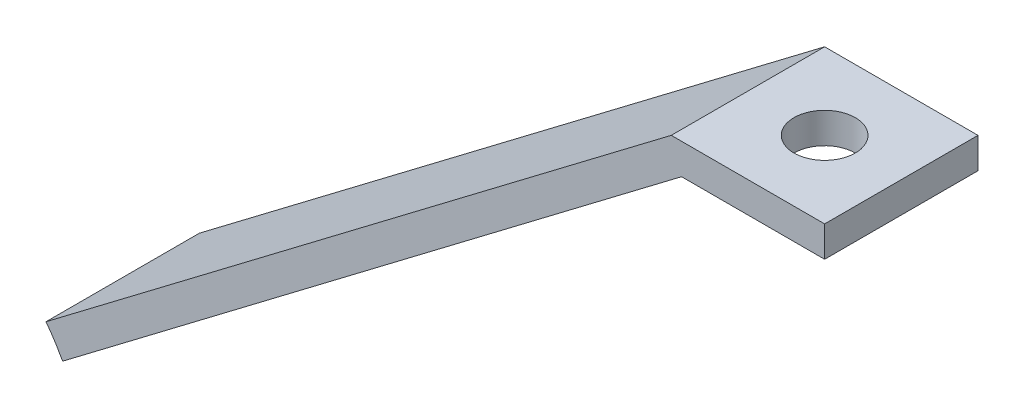
SolidWorks part; units mm, degrees
material "1.4113(X6CrMoS17-1)"
ref_plane "Płaszczyzna XY" through (0, 0, 0) normal (0, 0, 1) x (1, 0, 0)
ref_plane "Płaszczyzna XZ" through (0, 0, 0) normal (0, 1, 0) x (1, 0, 0)
ref_plane "Płaszczyzna YZ" through (0, 0, 0) normal (1, 0, 0) x (0, 0, -1)
ref_plane "Płaszczyzna1" through (0, 0, 502.9993) normal (0, 0, -1) x (-1, 0, 0)
sketch "Szkic1" plane through (0, 0, 502.9993) normal (0, 0, -1) x (-1, 0, 0)
  line L0 (-929.814, -322.668) -> (-970.5827, -291.7593)
  line L1 (-970.5827, -291.7593) -> (-980.5827, -291.7593)
  line L3 (-980.5827, -291.7593) -> (-980.5827, -293.7593)
  line L4 (-980.5827, -293.7593) -> (-971.2551, -293.7593)
  line L5 (-971.2551, -293.7593) -> (-930.8992, -324.3551)
  spline S0 degree 3 poles (-920, -317.7171) (-945, -317.7171) (-945, -343.7293) (-920, -343.7293) (-895, -343.7293) (-895, -317.7171) (-920, -317.7171) (-945, -317.7171) (-945, -343.7293) knots -0.5 0 0 0 0.5 0.5 0.5 1 1 1 1.5 1.5 1.5 weights 1 0.333333 0.333333 1 0.333333 0.333333 1 0.333333 0.333333 only from (-920, -317.7171) to (-920, -317.7171)
  spline S1 degree 3 poles (-929.814, -322.668) (-930.2144, -323.1961) (-930.5776, -323.7592) (-930.8992, -324.3551) knots 0.163264 0.163264 0.163264 0.163264 0.18461 0.18461 0.18461 0.18461 weights 0.560186 0.550311 0.541651 0.534207
  dimension "D1" = 10
  dimension "D2" = 2
  dimension "D3" = 2
  dimension "D4" = 980.5827
  dimension "D5" = 970.5827
  dimension "D6" = 291.7593
  dimension "D7" = 51.1608
extrude "Dodanie-wyciągnięcie1" add sketch "Szkic1" along normal blind 10
ref_plane "Płaszczyzna2" through (0, -293.7593, 0) normal (0, -1, 0) x (-1, 0, 0)
sketch "Szkic2" plane through (0, -293.7593, 0) normal (0, -1, 0) x (-1, 0, 0)
  line L0 (-980.5827, -492.9993) -> (-980.5827, -502.9993) construction
  line L1 (-980.5827, -502.9993) -> (-971.2551, -502.9993) construction
  circle A0 centre (-975.5827, -497.9993) radius 2
  dimension "D1" = 4
  dimension "D2" = 5
  dimension "D3" = 5
extrude "Wytnij-wyciągnięcie1" cut sketch "Szkic2" against normal blind 10
